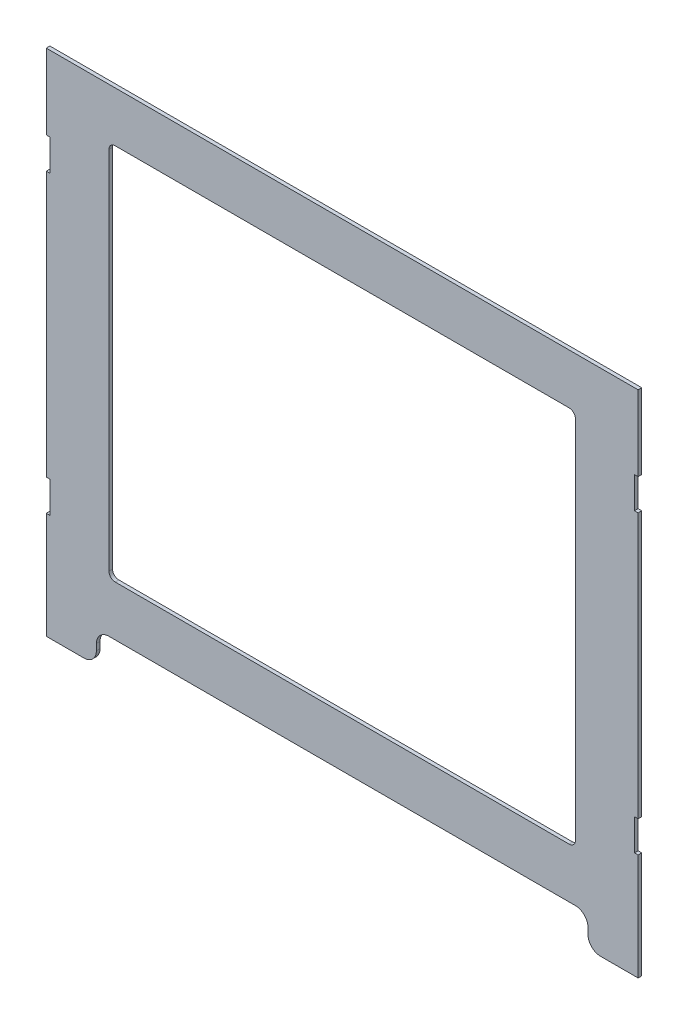
SolidWorks part; units mm, degrees
ref_plane "Front Plane" through (0, 0, 0) normal (0, 0, 1) x (1, 0, 0)
ref_plane "Top Plane" through (0, 0, 0) normal (0, 1, 0) x (1, 0, 0)
ref_plane "Right Plane" through (0, 0, 0) normal (1, 0, 0) x (0, 0, -1)
sketch "Sketch1" plane through (0, 0, 0) normal (0, 0, 1) x (1, 0, 0)
  line L0 (206.1, -203.2) -> (236.1, -203.2)
  line L1 (-236.1, -203.2) -> (-206.1, -203.2)
  line L2 (-236.1, -203.2) -> (-236.1, -118.2)
  line L3 (-236.1, 203.2) -> (236.1, 203.2)
  line L4 (236.1, -203.2) -> (236.1, -118.2)
  line L5 (-236.1, -203.2) -> (236.1, 203.2) construction
  line L6 (-236.1, 203.2) -> (236.1, -203.2) construction
  line L7 (236.1, 143.2) -> (236.1, 203.2)
  line L8 (-196.1, -193.2) -> (-196.1, -188.2)
  line L9 (-186.1, -178.2) -> (186.1, -178.2)
  line L10 (196.1, -193.2) -> (196.1, -188.2)
  line L11 (236.1, 143.2) -> (233.2, 143.2)
  line L12 (236.1, -93.2) -> (236.1, 118.2)
  line L13 (236.1, 118.2) -> (233.2, 118.2)
  line L14 (233.2, 143.2) -> (233.2, 118.2)
  line L15 (236.1, -93.2) -> (233.2, -93.2)
  line L16 (0, 203.2) -> (0, -178.2) construction
  line L17 (236.1, -118.2) -> (233.2, -118.2)
  line L18 (233.2, -93.2) -> (233.2, -118.2)
  line L19 (-236.1, -93.2) -> (-233.2, -93.2)
  line L20 (-233.2, -93.2) -> (-233.2, -118.2)
  line L21 (-236.1, -118.2) -> (-233.2, -118.2)
  line L22 (-236.1, 143.2) -> (-233.2, 143.2)
  line L23 (-233.2, 143.2) -> (-233.2, 118.2)
  line L24 (-236.1, 118.2) -> (-233.2, 118.2)
  line L25 (-236.1, 143.2) -> (-236.1, 203.2)
  line L26 (-236.1, -93.2) -> (-236.1, 118.2)
  arc A0 (-196.1, -188.2) -> (-186.1, -178.2) centre (-186.1, -188.2) cw
  arc A1 (-206.1, -203.2) -> (-196.1, -193.2) centre (-206.1, -193.2) ccw
  arc A2 (206.1, -203.2) -> (196.1, -193.2) centre (206.1, -193.2) cw
  arc A3 (186.1, -178.2) -> (196.1, -188.2) centre (186.1, -188.2) cw
  point P0 (0, 0)
  dimension "D6" = 10
  dimension "D1" = 406.4
  dimension "D2" = 472.2
  dimension "D3" = 25
  dimension "D4" = 40
  dimension "D5" = 40
  dimension "D7" = 2.9
  dimension "D8" = 60
  dimension "D9" = 25
  dimension "D10" = 25
  dimension "D11" = 2.9
  dimension "D12" = 85
extrude "Boss-Extrude1" add sketch "Sketch1" along normal blind 2.9
sketch "Sketch2" plane through (0, 0, 2.9) normal (0, 0, 1) x (1, 0, 0)
  line L0 (236.1, 203.2) -> (-236.1, 203.2) construction
  line L1 (-181.1, 163.2) -> (181.1, 163.2)
  line L2 (-186.1, 158.2) -> (-186.1, -133.2)
  line L3 (-181.1, -138.2) -> (181.1, -138.2)
  line L4 (186.1, 158.2) -> (186.1, -133.2)
  line L5 (-186.1, 163.2) -> (186.1, -138.2) construction
  line L6 (-186.1, -138.2) -> (186.1, 163.2) construction
  line L7 (236.1, -93.2) -> (236.1, 118.2) construction
  line L8 (-236.1, 118.2) -> (-236.1, -93.2) construction
  line L9 (-186.1, -178.2) -> (186.1, -178.2) construction
  arc A0 (181.1, -138.2) -> (186.1, -133.2) centre (181.1, -133.2) ccw
  arc A1 (181.1, 163.2) -> (186.1, 158.2) centre (181.1, 158.2) cw
  arc A2 (-181.1, 163.2) -> (-186.1, 158.2) centre (-181.1, 158.2) ccw
  arc A3 (-186.1, -133.2) -> (-181.1, -138.2) centre (-181.1, -133.2) ccw
  point P0 (0, 12.5)
  point P9 (-236.1, 12.5)
  dimension "D5" = 5
  dimension "D1" = 40
  dimension "D2" = 50
  dimension "D3" = 50
  dimension "D4" = 40
extrude "Cut-Extrude1" cut sketch "Sketch2" against normal through all
